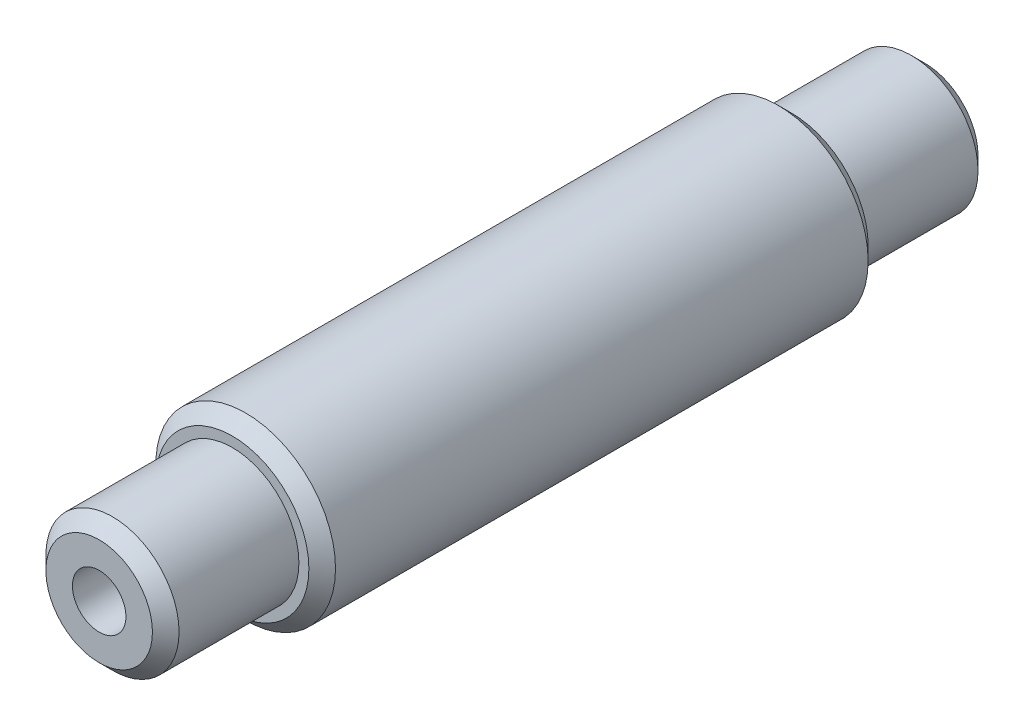
SolidWorks part; units mm, degrees
ref_plane "Front Plane" through (0, 0, 0) normal (0, 0, 1) x (1, 0, 0)
ref_plane "Top Plane" through (0, 0, 0) normal (0, 1, 0) x (1, 0, 0)
ref_plane "Right Plane" through (0, 0, 0) normal (1, 0, 0) x (0, 0, -1)
sketch "Sketch1" plane through (0, 0, 0) normal (0, 0, 1) x (1, 0, 0)
  circle A0 centre (0, 0) radius 8.5725
  circle A1 centre (0, 0) radius 6.35
  dimension "D1" = 17.145
  dimension "D2" = 12.7
extrude "Boss-Extrude1" add sketch "Sketch1" along normal mid plane 53.34
sketch "Sketch2" plane through (0, 0, 0) normal (0, 0, 1) x (1, 0, 0)
  circle A0 centre (0, 0) radius 6.35
  dimension "D1" = 12.7
extrude "Boss-Extrude2" add sketch "Sketch2" along normal mid plane 78.74
chamfer "Chamfer1" distance 1.27 angle 45 4 edges at (8.5725, 0, 26.67) (6.35, 0, 39.37) (6.35, 0, -39.37) (8.5725, 0, -26.67)
hole_wizard "1/4-20 Tapped Hole1" positions "Sketch6" profile "Sketch7" tap size "1/4-20" standard "ANSI Inch"
sketch "Sketch6" plane through (0, 0, -39.37) normal (0, 0, -1) x (-1, 0, 0)
  point P0 (0, 0)
sketch "Sketch7" plane through (0, 0, -39.37) normal (1, 0, 0) x (0, 1, 0)
  line L0 (0, 0) -> (0, 26.9338)
  line L1 (0, 26.9338) -> (2.5527, 25.4)
  line L2 (2.5527, 25.4) -> (2.5527, 0)
  line L5 (2.5527, 0) -> (0, 0)
  line L10 (0, 26.9338) -> (-2.5527, 25.4) construction
  line L11 (0, -6.35) -> (0, 107.95) construction
  dimension "Tap Drill Dia." = 5.1054
  dimension "Tap Drill Depth" = 25.4
  dimension "Drill Angle" = 118
cosmetic thread "Hole Thread1" parameters "D1"=19.05, "D2"=6.35
hole_wizard "1/4-20 Tapped Hole2" positions "Sketch8" profile "Sketch9" tap size "1/4-20" standard "ANSI Inch"
sketch "Sketch8" plane through (0, 0, 39.37) normal (0, 0, 1) x (1, 0, 0)
  point P0 (0, 0)
sketch "Sketch9" plane through (0, 0, 39.37) normal (1, 0, 0) x (0, -1, 0)
  line L0 (0, 0) -> (0, 26.9338)
  line L1 (0, 26.9338) -> (2.5527, 25.4)
  line L2 (2.5527, 25.4) -> (2.5527, 0)
  line L5 (2.5527, 0) -> (0, 0)
  line L10 (0, 26.9338) -> (-2.5527, 25.4) construction
  line L11 (0, -6.35) -> (0, 107.95) construction
  dimension "Tap Drill Dia." = 5.1054
  dimension "Tap Drill Depth" = 25.4
  dimension "Drill Angle" = 118
cosmetic thread "Hole Thread2" parameters "D1"=19.05, "D2"=6.35
